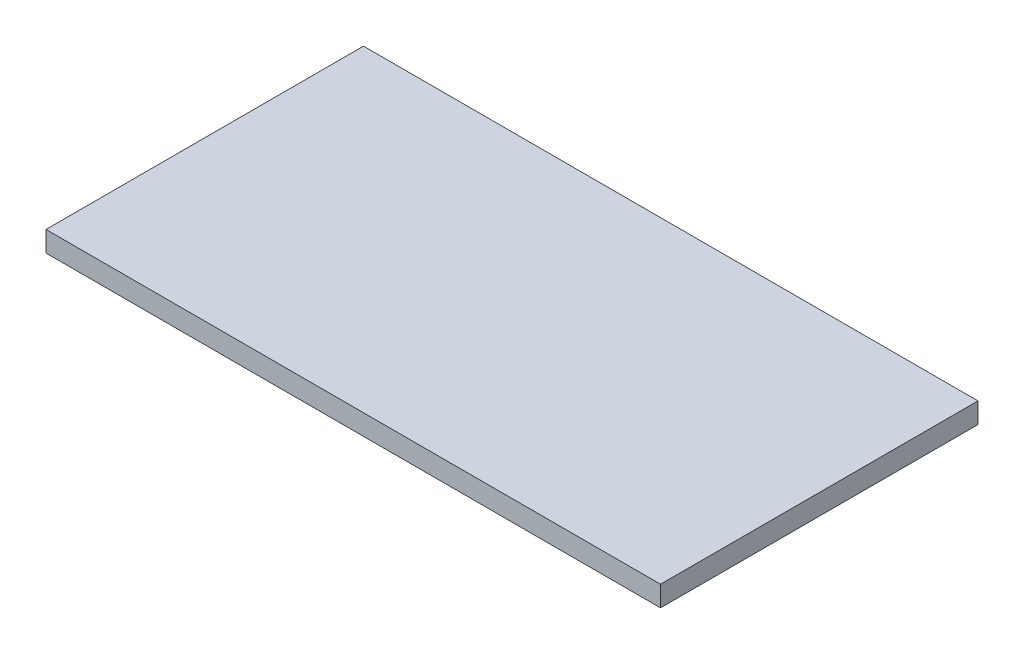
SolidWorks part; units mm, degrees
ref_plane "Front Plane" through (0, 0, 0) normal (0, 0, 1) x (1, 0, 0)
ref_plane "Top Plane" through (0, 0, 0) normal (0, 1, 0) x (1, 0, 0)
ref_plane "Right Plane" through (0, 0, 0) normal (1, 0, 0) x (0, 0, -1)
sketch "Sketch1" plane through (0, 0, 0) normal (0, 1, 0) x (1, 0, 0)
  line L1 (0, 0) -> (60, 0)
  line L2 (0, 0) -> (0, -31)
  line L3 (0, -31) -> (60, -31)
  line L4 (60, 0) -> (60, -31)
  point P4 (15, -15.5)
  point P5 (45, -15.5)
  point P7 (30, -7.5)
  point P8 (30, 0)
  dimension "D1" = 60
  dimension "D2" = 31
  dimension "D3" = 15.5
  dimension "D4" = 15
  dimension "D5" = 15
  dimension "D6" = 15.5
  dimension "D7" = 30
  dimension "D8" = 7.5
extrude "Boss-Extrude2" add sketch "Sketch1" against normal blind 2
